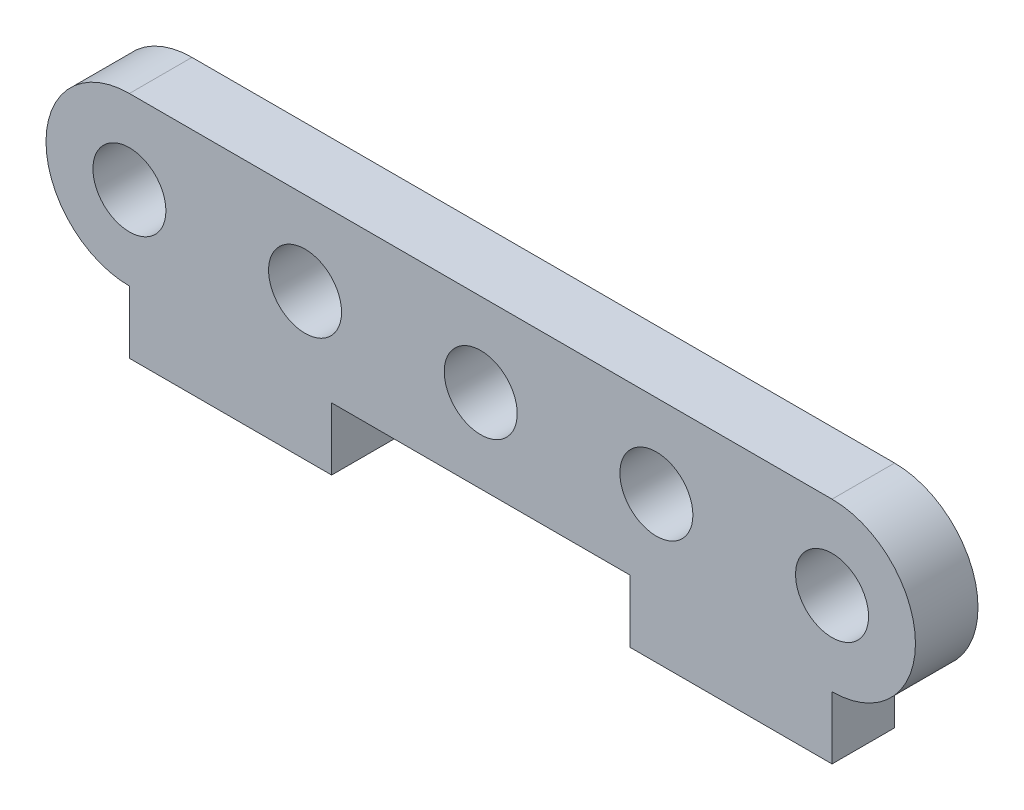
SolidWorks part; units mm, degrees
material "Balsa"
ref_plane "Front Plane" through (0, 0, 0) normal (0, 0, 1) x (1, 0, 0)
ref_plane "Top Plane" through (0, 0, 0) normal (0, 1, 0) x (1, 0, 0)
ref_plane "Right Plane" through (0, 0, 0) normal (1, 0, 0) x (0, 0, -1)
sketch "Sketch1" plane through (0, 0, 0) normal (0, 0, 1) x (1, 0, 0)
  line L0 (0, 18.4595) -> (0, -19.5095) construction
  line L1 (-16.85, 4) -> (16.85, 4)
  line L3 (-7.15, -4) -> (7.15, -4)
  line L5 (-16.85, 4) -> (16.85, -4) construction
  line L6 (-16.85, -4) -> (16.85, 4) construction
  line L8 (7.15, -4) -> (7.15, -7)
  line L9 (7.15, -7) -> (16.85, -7)
  line L10 (16.85, -4) -> (16.85, -7)
  line L14 (-16.85, -4) -> (-16.85, -7)
  line L15 (-16.85, -7) -> (-7.15, -7)
  line L16 (-7.15, -4) -> (-7.15, -7)
  arc A0 (-16.85, 4) -> (-16.85, -4) centre (-16.85, 0) ccw
  arc A1 (16.85, -4) -> (16.85, 4) centre (16.85, 0) ccw
  circle A2 centre (-16.85, 0) radius 1.75
  circle A3 centre (-8.425, 0) radius 1.75
  circle A4 centre (0, 0) radius 1.75
  circle A5 centre (8.425, 0) radius 1.75
  circle A6 centre (16.85, 0) radius 1.75
  point P0 (0, 0)
  point P8 (12, -7)
  point P24 (-12, -7)
  dimension "D2" = 4
  dimension "D11" = 3.5
  dimension "D5" = 9.7
  dimension "D6" = 9.7
  dimension "D1" = 3
  dimension "D7" = 3
  dimension "D3" = 33.7
  dimension "D10" = 8.425
  dimension "D4" = 12
  dimension "D8" = 12
  dimension "D9" = 5
extrude "Boss-Extrude1" add sketch "Sketch1" along normal blind 3
equation "\"D10@Sketch1\"=\"D3@Sketch1\"/(\"D9@Sketch1\"-1)"
equation "\"D8@Sketch1\"=\"D4@Sketch1\""
